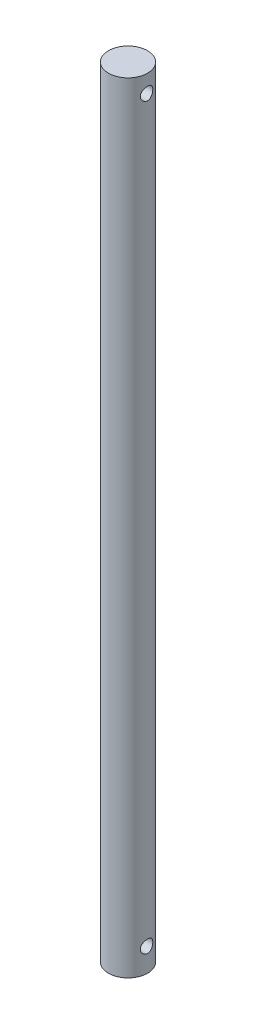
SolidWorks part; units mm, degrees
ref_plane "Front Plane" through (0, 0, 0) normal (0, 0, 1) x (1, 0, 0)
ref_plane "Top Plane" through (0, 0, 0) normal (0, 1, 0) x (1, 0, 0)
ref_plane "Right Plane" through (0, 0, 0) normal (1, 0, 0) x (0, 0, -1)
sketch "Sketch1" plane through (0, 0, 0) normal (1, 0, 0) x (0, 0, -1)
  line L1 (0, 0) -> (-10, 0)
  line L2 (0, 0) -> (0, 399.034)
  line L3 (0, 399.034) -> (-10, 399.034)
  line L4 (-10, 0) -> (-10, 399.034)
  circle A0 centre (0, 390.034) radius 3.2
  circle A1 centre (0, 12) radius 3.2
  dimension "D3" = 6.4
  dimension "D4" = 6.4
  dimension "D1" = 399.034
  dimension "D2" = 10
  dimension "D5" = 9
  dimension "D6" = 12
revolve "Revolve2" add sketch "Sketch1" angle 360 about L2
sketch "Sketch2" plane through (0, 0, 0) normal (1, 0, 0) x (0, 0, -1)
  line L0 (-10, 0) -> (10, 0) construction
  line L1 (10, 399.034) -> (-10, 399.034) construction
  line L2 (0, 12) -> (0, 390.034) construction
  line L3 (10, 0) -> (10, 399.034) construction
  circle A0 centre (0, 390.034) radius 3.2
  circle A1 centre (0, 12) radius 3.2
  dimension "D1" = 6.4
  dimension "D2" = 6.4
  dimension "D3" = 12
  dimension "D4" = 9
  dimension "D5" = 10
extrude "Cut-Extrude1" cut sketch "Sketch2" against normal through all both and the other way through all
